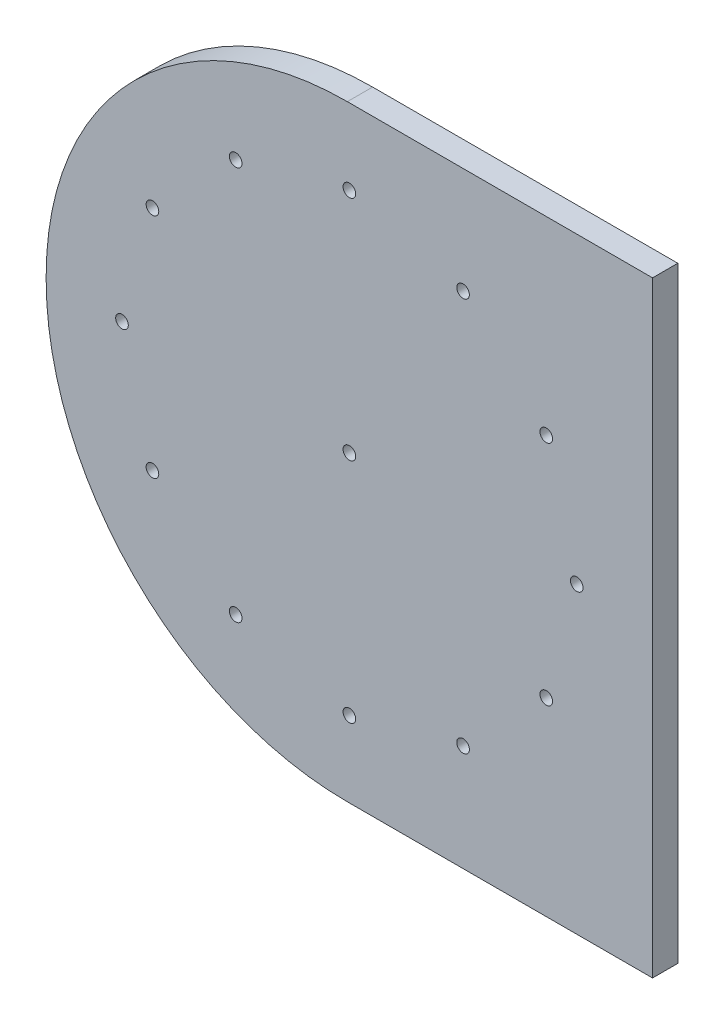
SolidWorks part; units mm, degrees
ref_plane "Front Plane" through (0, 0, 0) normal (0, 0, 1) x (1, 0, 0)
ref_plane "Top Plane" through (0, 0, 0) normal (0, 1, 0) x (1, 0, 0)
ref_plane "Right Plane" through (0, 0, 0) normal (1, 0, 0) x (0, 0, -1)
sketch "Sketch2" plane through (0, 0, 0) normal (0, 0, 1) x (1, 0, 0)
  line L0 (76.2, 0) -> (76.2, -76.2)
  line L1 (37.846, 0) -> (76.2, 0)
  line L2 (0, -37.846) -> (0, -38.354)
  line L3 (37.846, -76.2) -> (76.2, -76.2)
  arc A2 (0, -38.354) -> (37.846, -76.2) centre (37.846, -38.354) ccw
  arc A3 (0, -37.846) -> (37.846, 0) centre (37.846, -37.846) cw
  point P14 (0, 0)
  dimension "D1" = 76.2
  dimension "D4" = 76.2
extrude "Boss-Extrude1" add sketch "Sketch2" along normal blind 3.175
sketch "Sketch5" plane through (0, 0, 0) normal (0, 0, 1) x (1, 0, 0)
  line L0 (-1000, -38.1) -> (49000, -38.1) construction
  line L1 (0, -37.846) -> (0, -38.354) construction
  circle A0 centre (38.1, -38.1) radius 0.7937
  circle A1 centre (38.1, -38.1) radius 28.575 construction
  circle A2 centre (66.675, -38.1) radius 0.7937
  circle A3 centre (62.8467, -52.3875) radius 0.7937
  circle A4 centre (52.3875, -62.8467) radius 0.7937
  circle A5 centre (38.1, -66.675) radius 0.7938
  circle A6 centre (23.8125, -62.8467) radius 0.7938
  circle A7 centre (13.3533, -52.3875) radius 0.7937
  circle A8 centre (9.525, -38.1) radius 0.7937
  circle A9 centre (13.3533, -23.8125) radius 0.7938
  circle A10 centre (23.8125, -13.3533) radius 0.7937
  circle A11 centre (38.1, -9.525) radius 0.7937
  circle A12 centre (52.3875, -13.3533) radius 0.7937
  circle A13 centre (62.8467, -23.8125) radius 0.7937
  point P5 (0, -38.1)
  point P41 (38.1, -38.1)
  dimension "D2" = 1.5875
  dimension "D3" = 57.15
  dimension "D4" = 1.5875
  dimension "D1" = 38.1
  dimension "D5" = 12
extrude "Cut-Extrude10" cut sketch "Sketch5" along normal blind 19.05
